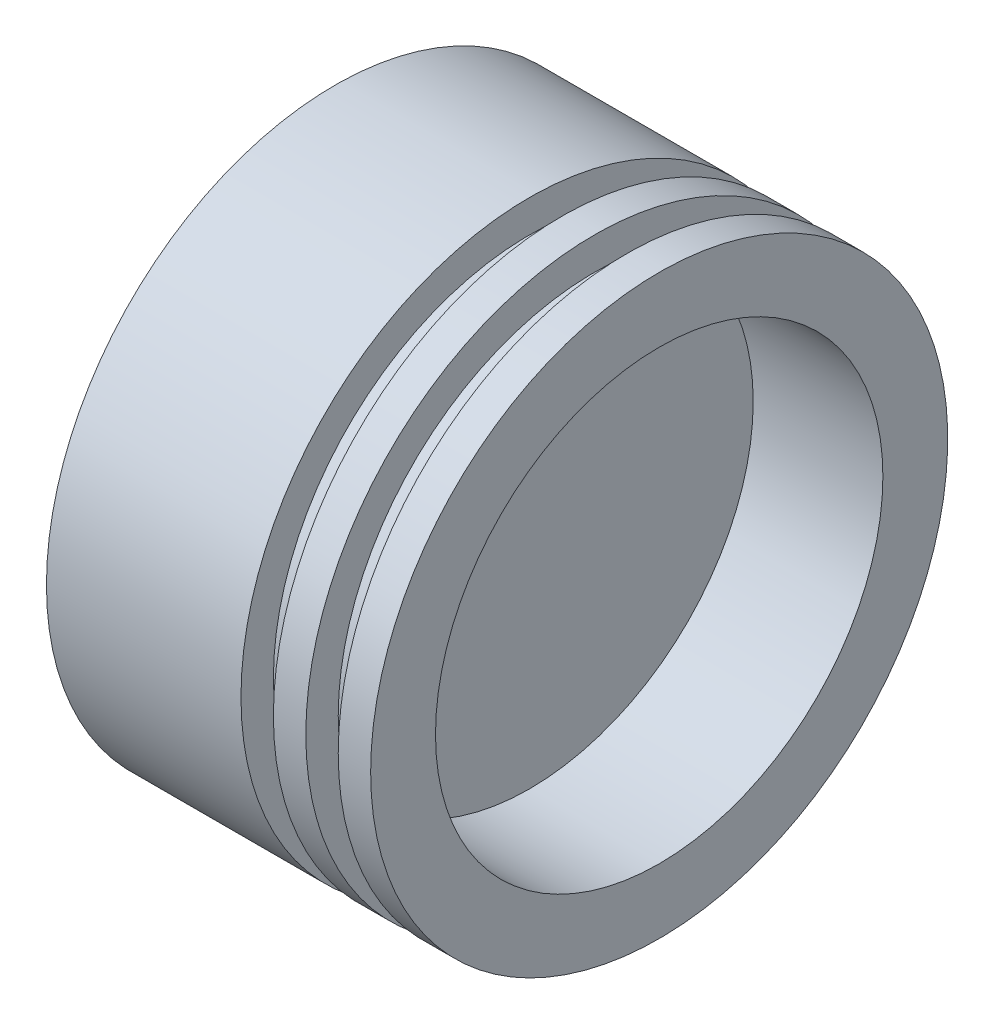
SolidWorks part; units mm, degrees
material "6063-T6"
ref_plane "Front Plane" through (0, 0, 0) normal (0, 0, 1) x (1, 0, 0)
ref_plane "Top Plane" through (0, 0, 0) normal (0, 1, 0) x (1, 0, 0)
ref_plane "Right Plane" through (0, 0, 0) normal (1, 0, 0) x (0, 0, -1)
sketch "Sketch1" plane through (0, 0, 0) normal (0, 0, 1) x (1, 0, 0)
  line L0 (0, 0) -> (30, 0) construction
  line L1 (0, 0) -> (0, 44.5)
  line L2 (0, 44.5) -> (30, 44.5)
  line L7 (30, 44.5) -> (30, 39.5)
  line L8 (30, 39.5) -> (35, 39.5)
  line L9 (35, 39.5) -> (35, 44.5)
  line L10 (35, 44.5) -> (40, 44.5)
  line L11 (40, 44.5) -> (40, 39.5)
  line L12 (40, 39.5) -> (45, 39.5)
  line L13 (45, 39.5) -> (45, 44.5)
  line L14 (45, 44.5) -> (50, 44.5)
  line L15 (50, 44.5) -> (50, 34.5)
  line L16 (50, 34.5) -> (30, 34.5)
  line L17 (30, 34.5) -> (30, 0)
  line L18 (30, 0) -> (0, 0)
  dimension "D1" = 50
  dimension "D2" = 44.5
  dimension "D3" = 5
  dimension "D4" = 5
  dimension "D5" = 5
  dimension "D7" = 10
  dimension "D8" = 20
revolve "Revolve1" add sketch "Sketch1" angle 360 about L0
